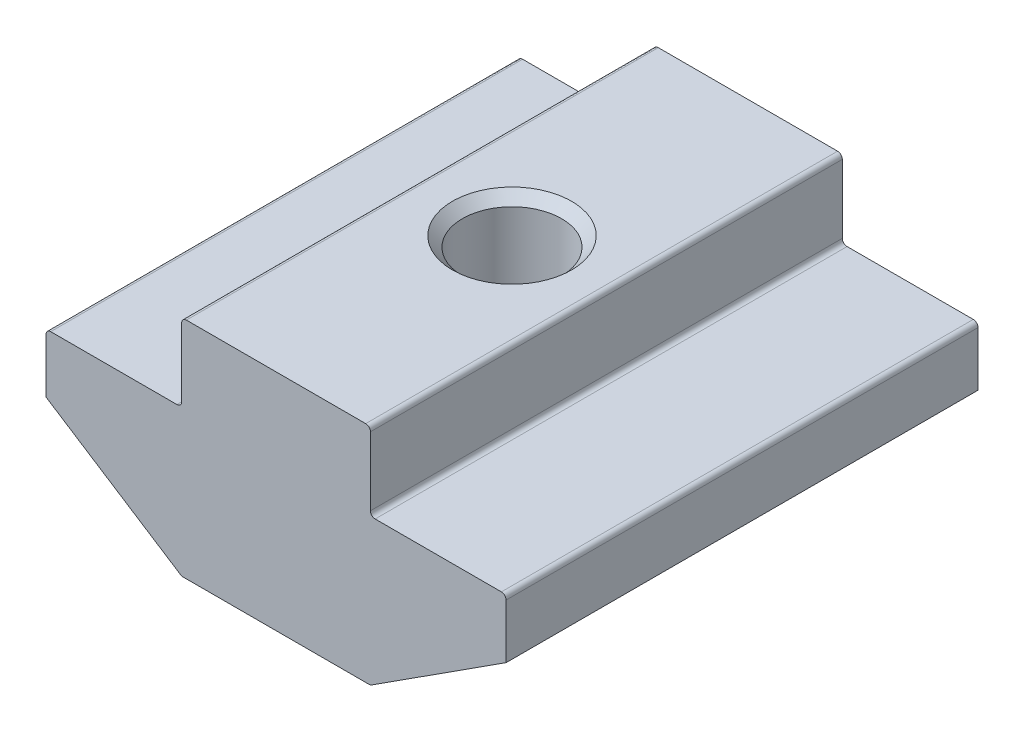
SolidWorks part; units mm, degrees
ref_plane "Спереди" through (0, 0, 0) normal (0, 0, 1) x (1, 0, 0)
ref_plane "Сверху" through (0, 0, 0) normal (0, 1, 0) x (1, 0, 0)
ref_plane "Справа" through (0, 0, 0) normal (1, 0, 0) x (0, 0, -1)
sketch "Эскиз1" plane through (0, 0, 0) normal (0, 0, 1) x (1, 0, 0)
  line L0 (4, 0) -> (-4, 0)
  line L1 (-4, 0) -> (-4, -3.3)
  line L2 (-4, -3.3) -> (-9.75, -3.3)
  line L3 (-9.75, -3.3) -> (-9.75, -5.8)
  line L4 (-9.75, -5.8) -> (-4, -9.5)
  line L5 (-4, -9.5) -> (4, -9.5)
  line L6 (0, -9.5) -> (0, 0) construction
  line L7 (9.75, -5.8) -> (4, -9.5)
  line L8 (9.75, -3.3) -> (9.75, -5.8)
  line L9 (4, -3.3) -> (9.75, -3.3)
  line L10 (4, 0) -> (4, -3.3)
  point P3 (-4, -1.65)
  dimension "D1" = 8
  dimension "D2" = 19.5
  dimension "D3" = 2.5
  dimension "D4" = 9.5
  dimension "D5" = 6.2
extrude "Бобышка-Вытянуть1" add sketch "Эскиз1" along normal mid plane 20
hole_wizard "Отверстие обработанное метчиком M53" positions "Эскиз2" profile "Эскиз4" tap size "M5" standard "ISO" end condition through all
sketch "Эскиз2" plane through (0, 0, 0) normal (0, 1, 0) x (1, 0, 0)
  point P0 (0, 0)
sketch "Эскиз4" plane through (0, 0, 0) normal (1, 0, 0) x (0, 0, 1)
  line L0 (0, 0) -> (0, 9.5)
  line L1 (0, 9.5) -> (2.525, 9.5)
  line L2 (2.1, 9.075) -> (2.1, 0.425)
  line L3 (2.1, 0.425) -> (2.525, 0)
  line L5 (2.525, 0) -> (0, 0)
  line L6 (-2.1, 0.425) -> (-2.525, 0) construction
  line L7 (2.525, 9.5) -> (2.1, 9.075)
  line L8 (-2.525, 9.5) -> (-2.1, 9.075) construction
  line L11 (0, -6.35) -> (0, 107.95) construction
  dimension "Диаметр проходного сверла" = 4.2
  dimension "Глубина проходного сверла" = 9.5
  dimension "Диаметр передней зенковки" = 5.05
  dimension "Угол передней зенковки" = 90
  dimension "Диаметр задней зенковки" = 5.05
  dimension "Угол задней зенковки" = 90
cosmetic thread "Отверстие резьбы1" parameters "D2"=5
fillet "Скругление1" radius 0.2 8 edges at (4, -9.5, 0) (-4, -9.5, 0) (9.75, -3.3, 0) (4, -3.3, 0) (4, 0, 0) (-4, 0, 0) (-9.75, -3.3, 0) (-4, -3.3, 0)
